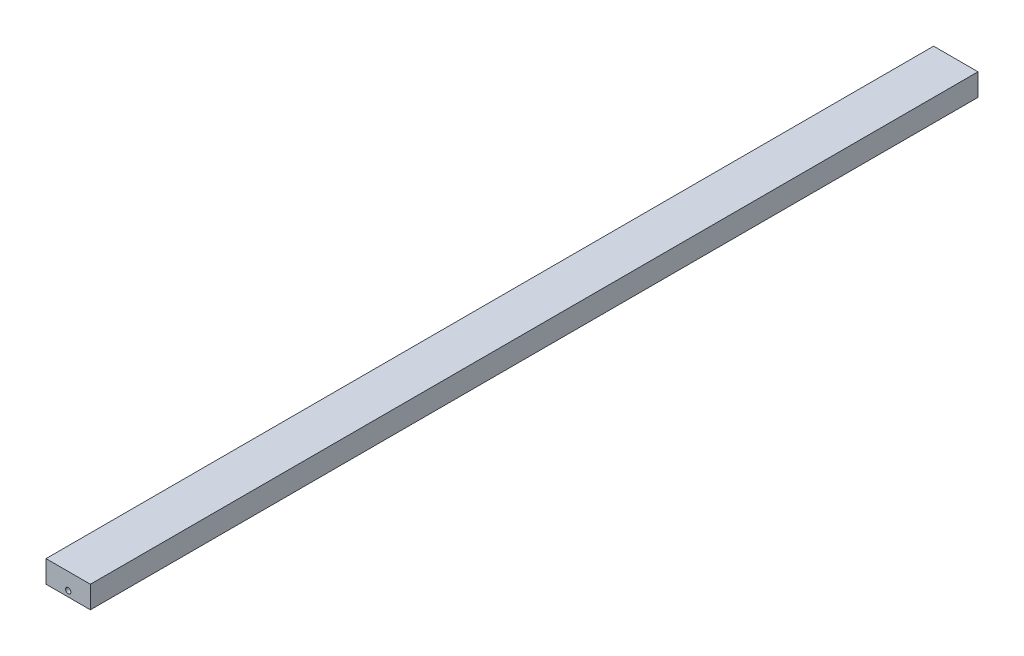
SolidWorks part; units mm, degrees
ref_plane "Ebene vorne" through (0, 0, 0) normal (0, 0, 1) x (1, 0, 0)
ref_plane "Ebene oben" through (0, 0, 0) normal (0, 1, 0) x (1, 0, 0)
ref_plane "Ebene rechts" through (0, 0, 0) normal (1, 0, 0) x (0, 0, -1)
sketch "Skizze1" plane through (0, 0, 0) normal (0, 0, 1) x (1, 0, 0)
  line L1 (-5, 2.5) -> (5, 2.5)
  line L2 (-5, 2.5) -> (-5, -2.5)
  line L3 (-5, -2.5) -> (5, -2.5)
  line L4 (5, 2.5) -> (5, -2.5)
  line L5 (-5, 2.5) -> (5, -2.5) construction
  line L6 (-5, -2.5) -> (5, 2.5) construction
  point P0 (0, 0)
  dimension "D1" = 10
  dimension "D2" = 5
extrude "Aufsatz-Linear austragen1" add sketch "Skizze1" along normal blind 200
sketch "Skizze2" plane through (0, 0, 0) normal (0, 0, 1) x (1, 0, 0)
  line L0 (0, -2.75) -> (0, 2.75) construction
  circle A0 centre (0, -1.25) radius 0.6
  dimension "D1" = 1.2
  dimension "D2" = 1.25
extrude "Schnitt-Linear austragen1" cut sketch "Skizze2" along normal through all
sketch "Skizze3" plane through (0, 0, 0) normal (0, 0, 1) x (1, 0, 0)
  line L0 (0.6, -1.25) -> (-0.6, -1.25)
  circle A0 centre (0, -1.25) radius 0.6 construction
  point P4 (0, -1.25)
  dimension "D1" = 1.25
split line "Trennlinie1"
